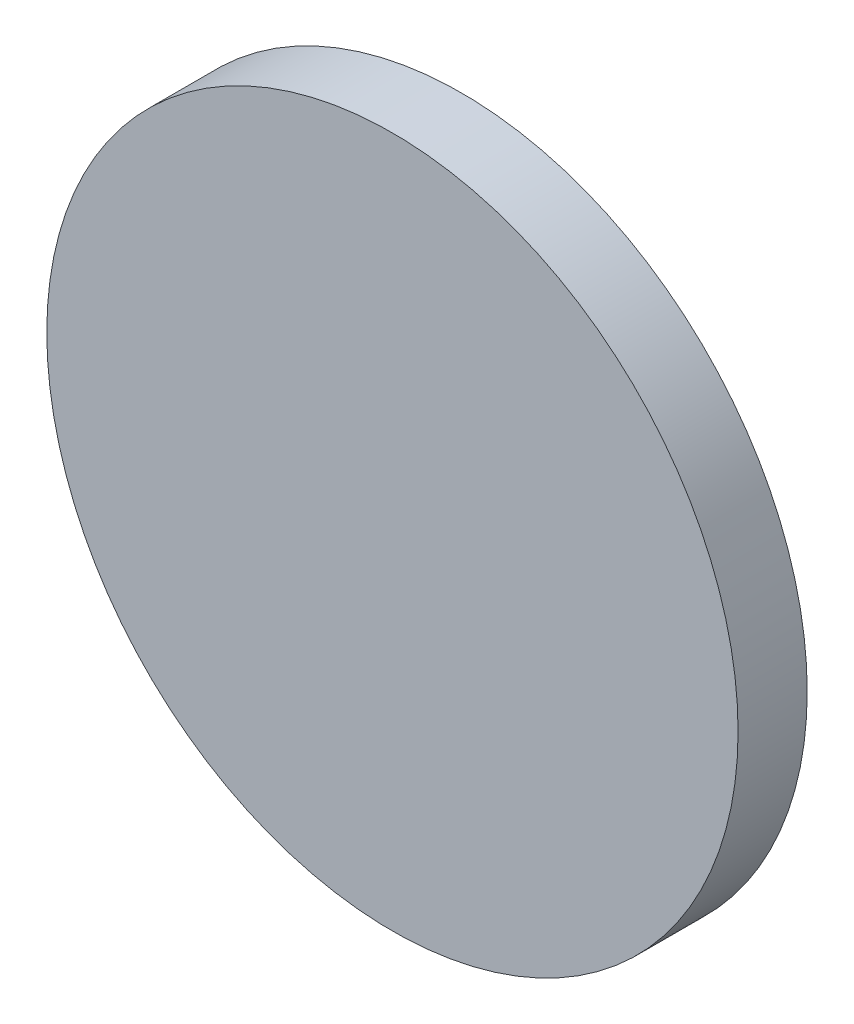
SolidWorks part; units mm, degrees
ref_plane "Front Plane" through (0, 0, 0) normal (0, 0, 1) x (1, 0, 0)
ref_plane "Top Plane" through (0, 0, 0) normal (0, 1, 0) x (1, 0, 0)
ref_plane "Right Plane" through (0, 0, 0) normal (1, 0, 0) x (0, 0, -1)
sketch "Sketch1" plane through (0, 0, 0) normal (0, 0, 1) x (1, 0, 0)
  circle A0 centre (0, 0) radius 5
extrude "Boss-Extrude1" add sketch "Sketch1" along normal blind 1
